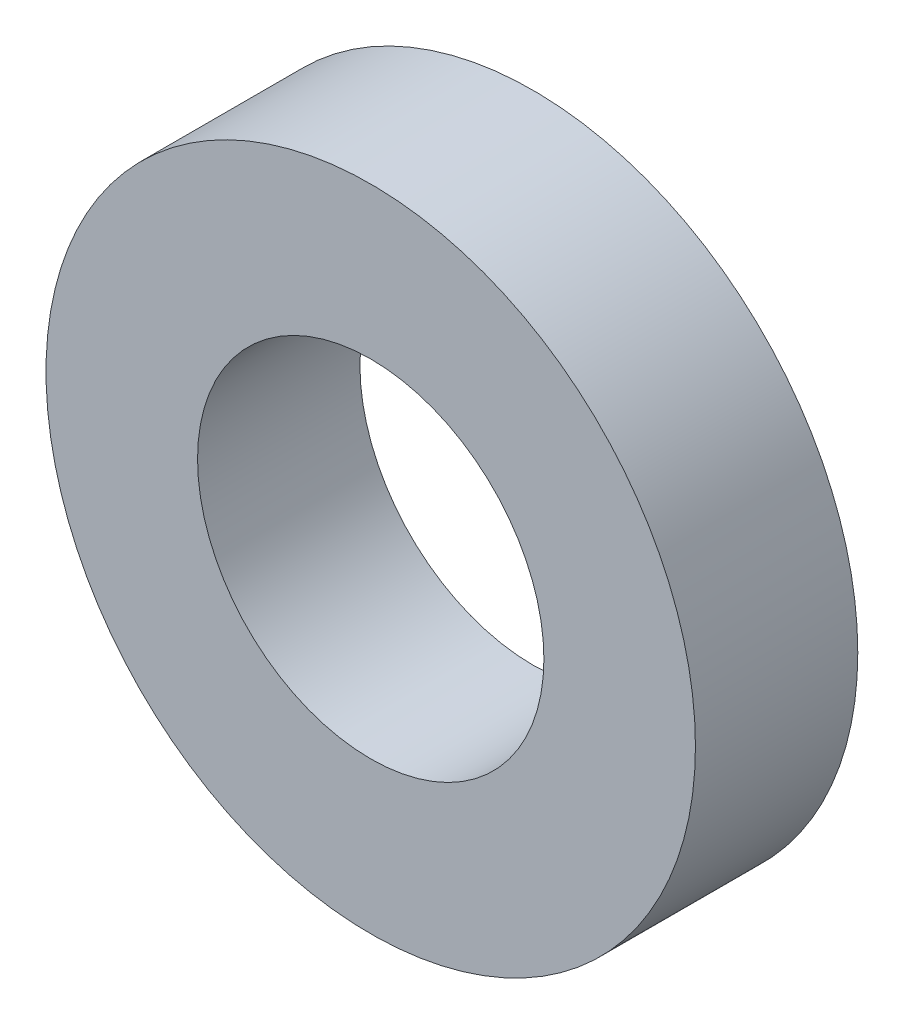
SolidWorks part; units mm, degrees
ref_plane "Front Plane" through (0, 0, 0) normal (1, 0, 0) x (0, 1, 0)
ref_plane "Top Plane" through (0, 0, 0) normal (0, 0, 1) x (0, 1, 0)
ref_plane "Right Plane" through (0, 0, 0) normal (0, 1, 0) x (-1, 0, 0)
sketch "Sketch1" plane through (0, 0, 0) normal (0, 0, 1) x (0, 1, 0)
  circle A0 centre (0, 0) radius 1.6
  circle A1 centre (0, 0) radius 3
  dimension "D1" = 3.2
  dimension "D2" = 6
extrude "Boss-Extrude1" add sketch "Sketch1" along normal blind 1.5
